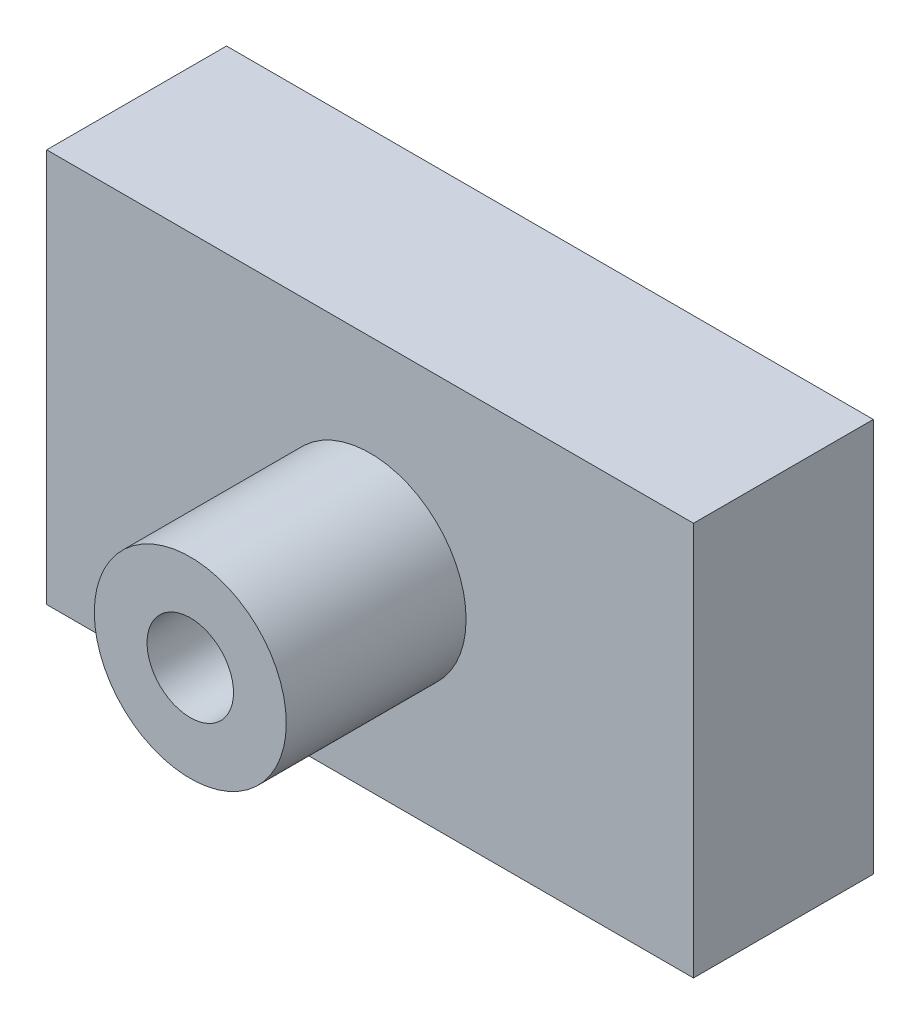
SolidWorks part; units mm, degrees
ref_plane "Front Plane" through (0, 0, 0) normal (0, 0, 1) x (1, 0, 0)
ref_plane "Top Plane" through (0, 0, 0) normal (0, 1, 0) x (1, 0, 0)
ref_plane "Right Plane" through (0, 0, 0) normal (1, 0, 0) x (0, 0, -1)
sketch "Sketch1" plane through (0, 0, 0) normal (0, 0, 1) x (1, 0, 0)
  line L1 (-28.7762, 17.5215) -> (28.7762, 17.5215)
  line L2 (-28.7762, 17.5215) -> (-28.7762, -17.5215)
  line L3 (-28.7762, -17.5215) -> (28.7762, -17.5215)
  line L4 (28.7762, 17.5215) -> (28.7762, -17.5215)
  line L5 (-28.7762, 17.5215) -> (28.7762, -17.5215) construction
  line L6 (-28.7762, -17.5215) -> (28.7762, 17.5215) construction
  point P0 (0, 0)
  point P6 (0, 0)
extrude "Boss-Extrude1" add sketch "Sketch1" along normal blind 16
sketch "Sketch2" plane through (0, 0, 16) normal (0, 0, 1) x (1, 0, 0)
  circle A0 centre (0, 0) radius 8.5409
extrude "Boss-Extrude2" add sketch "Sketch2" along normal blind 16
sketch "Sketch3" plane through (0, 0, 32) normal (0, 0, 1) x (1, 0, 0)
  circle A0 centre (0, 0) radius 3.847
extrude "Cut-Extrude1" cut sketch "Sketch3" against normal blind 39
